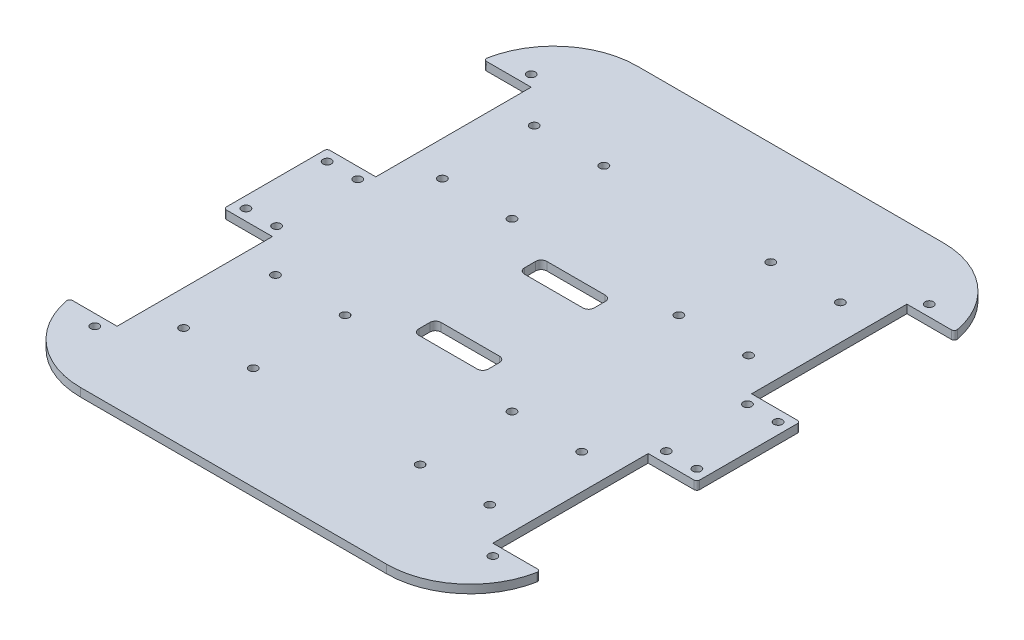
SolidWorks part; units mm, degrees
ref_plane "Front Plane" through (0, 0, 0) normal (0, 0, 1) x (1, 0, 0)
ref_plane "Top Plane" through (0, 0, 0) normal (0, 1, 0) x (1, 0, 0)
ref_plane "Right Plane" through (0, 0, 0) normal (1, 0, 0) x (0, 0, -1)
sketch "Sketch1" plane through (0, 0, 0) normal (0, 1, 0) x (1, 0, 0)
  line L1 (-85, 100) -> (85, 100)
  line L2 (-85, 100) -> (-85, -100)
  line L3 (-85, -100) -> (85, -100)
  line L4 (85, 100) -> (85, -100)
  line L5 (-85, 100) -> (85, -100) construction
  line L6 (-85, -100) -> (85, 100) construction
  point P0 (0, 0)
  dimension "D1" = 200
  dimension "D2" = 170
extrude "Boss-Extrude1" add sketch "Sketch1" along normal blind 3
sketch "Sketch2" plane through (0, 0, 0) normal (0, -1, 0) x (1, 0, 0)
  line L0 (-55, 62.98) -> (-55, 29.98) construction
  line L1 (-55, 29.98) -> (-29.98, 29.98) construction
  line L2 (-29.98, 29.98) -> (-29.98, 62.98) construction
  line L3 (-29.98, 62.98) -> (-55, 62.98) construction
  line L4 (-85, -100) -> (-85, 100) construction
  line L5 (29.98, 62.98) -> (55, 62.98) construction
  line L6 (55, 62.98) -> (55, 29.98) construction
  line L7 (55, 29.98) -> (29.98, 29.98) construction
  line L8 (29.98, 29.98) -> (29.98, 62.98) construction
  line L9 (29.98, 62.98) -> (55, 62.98) construction
  line L10 (29.98, -62.98) -> (55, -62.98) construction
  line L11 (55, -62.98) -> (55, -29.98) construction
  line L12 (55, -29.98) -> (29.98, -29.98) construction
  line L13 (29.98, -29.98) -> (29.98, -62.98) construction
  line L14 (-29.98, -29.98) -> (-29.98, -62.98) construction
  line L15 (-29.98, -62.98) -> (-55, -62.98) construction
  line L16 (-55, -62.98) -> (-55, -29.98) construction
  line L17 (-55, -29.98) -> (-29.98, -29.98) construction
  line L18 (-42.49, 62.98) -> (-42.49, 29.98) construction
  line L19 (42.49, 62.98) -> (42.49, 29.98) construction
  line L20 (85, 100) -> (85, -100) construction
  line L21 (85, -100) -> (-85, -100) construction
  line L22 (-85, 100) -> (85, 100) construction
  line L23 (42.49, -29.98) -> (42.49, -62.98) construction
  line L24 (-56.5, 62.98) -> (-53.5, 62.98) construction
  line L25 (-29.98, 62.98) -> (-55, 62.98) construction
  line L26 (-42.49, -29.98) -> (-42.49, -62.98) construction
  line L27 (29.98, -46.48) -> (55, -46.48) construction
  line L28 (-29.98, -46.48) -> (-55, -46.48) construction
  line L29 (29.98, 46.48) -> (55, 46.48) construction
  circle A0 centre (-55, 62.98) radius 1.5
  circle A1 centre (-55, 29.98) radius 1.5
  circle A2 centre (-29.98, 62.98) radius 1.5
  circle A3 centre (-29.98, 29.98) radius 1.5
  circle A4 centre (29.98, 62.98) radius 1.5
  circle A5 centre (55, 62.98) radius 1.5
  circle A6 centre (55, 29.98) radius 1.5
  circle A7 centre (29.98, 29.98) radius 1.5
  circle A8 centre (29.98, -62.98) radius 1.5
  circle A9 centre (29.98, -29.98) radius 1.5
  circle A10 centre (55, -62.98) radius 1.5
  circle A11 centre (55, -29.98) radius 1.5
  circle A12 centre (-29.98, -62.98) radius 1.5
  circle A13 centre (-55, -62.98) radius 1.5
  circle A14 centre (-55, -29.98) radius 1.5
  circle A15 centre (-29.98, -29.98) radius 1.5
  dimension "D1" = 30
  dimension "D3" = 25.02
  dimension "D6" = 30
  dimension "D2" = 30
  dimension "D4" = 0
  dimension "D5" = 30
  dimension "D7" = 37.02
  dimension "D8" = 37.02
  dimension "D9" = 37.02
  dimension "D10" = 33
  dimension "D11" = 25.02
  dimension "D12" = 25.02
  dimension "D13" = 33
  dimension "D14" = 25.02
  dimension "D15" = 33
  dimension "D16" = 59.96
  dimension "D17" = 59.96
extrude "Cut-Extrude1" cut sketch "Sketch2" against normal blind 43
fillet "Fillet1" radius 30 4 edges at (-85, 1.5, -100) (85, 1.5, -100) (-85, 1.5, 100) (85, 1.5, 100)
sketch "Sketch4" plane through (0, 0, 0) normal (0, -1, 0) x (1, 0, 0)
  line L0 (-55, 62.98) -> (-55, 29.98) construction
  line L1 (-55, 29.98) -> (-29.98, 29.98) construction
  line L2 (-29.98, 29.98) -> (-55, 62.98) construction
  line L3 (-55, 62.98) -> (-29.98, 62.98) construction
  line L4 (-29.98, 62.98) -> (-55, 29.98) construction
  line L5 (-29.98, 62.98) -> (-29.98, 29.98) construction
  line L6 (-67.5, 46.48) -> (-96.9, 46.48) construction
  line L7 (-67.5, 74.38) -> (-96.9, 74.38)
  line L8 (-67.5, 74.38) -> (-67.5, 18.58)
  line L9 (-67.5, 18.58) -> (-96.9, 18.58)
  line L10 (-96.9, 74.38) -> (-96.9, 18.58)
  line L11 (-29.98, 46.48) -> (-55, 46.48) construction
  line L12 (0, 100) -> (0, -100) construction
  line L13 (-55, 100) -> (55, 100) construction
  line L14 (55, -100) -> (-55, -100) construction
  line L15 (-85, 0) -> (85, 0) construction
  line L16 (-85, -70) -> (-85, 70) construction
  line L17 (85, 70) -> (85, -70) construction
  line L18 (67.5, 18.58) -> (96.9, 18.58)
  line L19 (96.9, 74.38) -> (96.9, 18.58)
  line L20 (67.5, 74.38) -> (96.9, 74.38)
  line L21 (67.5, 74.38) -> (67.5, 18.58)
  line L22 (67.5, -74.38) -> (67.5, -18.58)
  line L23 (67.5, -74.38) -> (96.9, -74.38)
  line L24 (96.9, -74.38) -> (96.9, -18.58)
  line L25 (67.5, -18.58) -> (96.9, -18.58)
  line L26 (-67.5, -18.58) -> (-96.9, -18.58)
  line L27 (-96.9, -74.38) -> (-96.9, -18.58)
  line L28 (-67.5, -74.38) -> (-96.9, -74.38)
  line L29 (-67.5, -74.38) -> (-67.5, -18.58)
  dimension "D1" = 55.8
  dimension "D2" = 29.4
  dimension "D3" = 12.5
extrude "Cut-Extrude4" cut sketch "Sketch4" against normal blind 10
fillet "Fillet3" radius 1 1 edges at (-84.6785, 1.5, 74.38)
fillet "Fillet4" radius 1 1 edges at (-85, 1.5, 18.58)
fillet "Fillet5" radius 1 1 edges at (84.6785, 1.5, 74.38)
fillet "Fillet6" radius 1 1 edges at (85, 1.5, 18.58)
fillet "Fillet7" radius 1 1 edges at (85, 1.5, -18.58)
fillet "Fillet8" radius 1 1 edges at (84.6785, 1.5, -74.38)
fillet "Fillet9" radius 1 1 edges at (-84.6785, 1.5, -74.38)
fillet "Fillet10" radius 1 1 edges at (-85, 1.5, -18.58)
sketch "Sketch5" plane through (0, 0, 0) normal (0, -1, 0) x (1, 0, 0)
  line L0 (-85, 0) -> (85, 0) construction
  line L1 (-85, -17.58) -> (-85, 17.58) construction
  line L2 (85, 17.58) -> (85, -17.58) construction
  line L3 (0, 100) -> (0, -100) construction
  line L4 (-55, 100) -> (55, 100) construction
  line L5 (55, -100) -> (-55, -100) construction
  line L6 (0, -15) -> (0, -23) construction
  line L7 (-12.5, -15) -> (12.5, -15)
  line L8 (-12.5, -15) -> (-12.5, -23)
  line L9 (-12.5, -23) -> (12.5, -23)
  line L10 (12.5, -15) -> (12.5, -23)
  line L11 (-12.5, 23) -> (12.5, 23)
  line L12 (12.5, 15) -> (12.5, 23)
  line L13 (-12.5, 15) -> (12.5, 15)
  line L14 (-12.5, 15) -> (-12.5, 23)
  dimension "D1" = 8
  dimension "D2" = 25
  dimension "D3" = 15
extrude "Cut-Extrude5" cut sketch "Sketch5" against normal blind 10
fillet "Fillet11" radius 2 3 edges at (-12.5, 1.5, -23) (-12.5, 1.5, -15) (12.5, 1.5, -15)
fillet "Fillet12" radius 2 1 edges at (12.5, 1.5, -23)
fillet "Fillet13" radius 2 1 edges at (12.5, 1.5, 15)
fillet "Fillet14" radius 2 1 edges at (12.5, 1.5, 23)
fillet "Fillet15" radius 2 1 edges at (-12.5, 1.5, 23)
fillet "Fillet16" radius 2 1 edges at (-12.5, 1.5, 15)
sketch "Sketch6" plane through (0, 0, 0) normal (0, -1, 0) x (1, 0, 0)
  line L0 (-75.75, 18.58) -> (-75.75, -18.58) construction
  line L1 (-84, 18.58) -> (-67.5, 18.58) construction
  line L2 (-67.5, -18.58) -> (-84, -18.58) construction
  line L3 (-85, 0) -> (85, 0) construction
  line L4 (-85, -17.58) -> (-85, 17.58) construction
  line L5 (0, 100) -> (0, -100) construction
  line L6 (-55, 100) -> (55, 100) construction
  line L7 (55, -100) -> (-55, -100) construction
  line L8 (75.75, 18.58) -> (75.75, -18.58) construction
  circle A0 centre (-81, -14.58) radius 1.5
  circle A1 centre (-81, 14.58) radius 1.5
  circle A2 centre (-70, 14.58) radius 1.5
  circle A3 centre (-70, -14.58) radius 1.5
  circle A4 centre (70, -14.58) radius 1.5
  circle A5 centre (70, 14.58) radius 1.5
  circle A6 centre (81, 14.58) radius 1.5
  circle A7 centre (81, -14.58) radius 1.5
  point P26 (0, 0)
  dimension "D1" = 4
  dimension "D2" = 4
  dimension "D3" = 4
  dimension "D4" = 4
  dimension "D5" = 4
  dimension "D6" = 4
  dimension "D7" = 11
  dimension "D8" = 11
extrude "Cut-Extrude6" cut sketch "Sketch6" against normal blind 10
sketch "Sketch7" plane through (0, 0, 0) normal (0, -1, 0) x (1, 0, 0)
  line L0 (-67.5, 74.38) -> (-67.5, 100.2692) construction
  line L1 (-67.5, 74.38) -> (-83.4966, 74.38) construction
  line L2 (0, 100) -> (0, -100) construction
  line L3 (-55, 100) -> (55, 100) construction
  line L4 (55, -100) -> (-55, -100) construction
  line L5 (85, 0) -> (-85, 0) construction
  line L6 (85, 17.58) -> (85, -17.58) construction
  line L7 (-85, -17.58) -> (-85, 17.58) construction
  line L8 (67.5, 74.38) -> (67.5, 100.2692) construction
  line L9 (67.5, -74.38) -> (67.5, -100.2692) construction
  line L10 (-67.5, -74.38) -> (-67.5, -100.2692) construction
  circle A0 centre (-71.5, 78.38) radius 1.5
  circle A1 centre (71.5, 78.38) radius 1.5
  circle A2 centre (71.5, -78.38) radius 1.5
  circle A3 centre (-71.5, -78.38) radius 1.5
  dimension "D1" = 4
  dimension "D2" = 4
extrude "Cut-Extrude8" cut sketch "Sketch7" against normal blind 10
